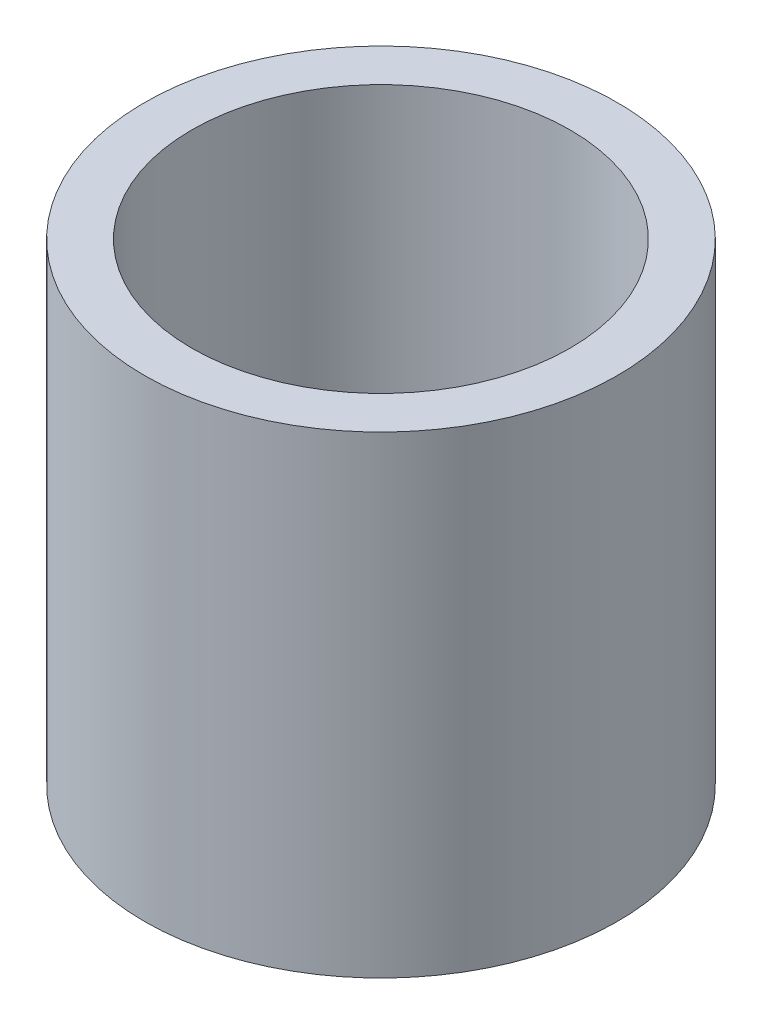
SolidWorks part; units mm, degrees
material "6061-T6 (SS)"
ref_plane "Front Plane" through (0, 0, 0) normal (0, 0, 1) x (1, 0, 0)
ref_plane "Top Plane" through (0, 0, 0) normal (0, 1, 0) x (1, 0, 0)
ref_plane "Right Plane" through (0, 0, 0) normal (1, 0, 0) x (0, 0, -1)
sketch "Sketch1" plane through (0, 0, 0) normal (0, 1, 0) x (1, 0, 0)
  circle A0 centre (0, 0) radius 3.175
  circle A1 centre (0, 0) radius 2.54
  dimension "D1" = 6.35
  dimension "D2" = 5.08
extrude "Boss-Extrude1" add sketch "Sketch1" along normal blind 6.35
